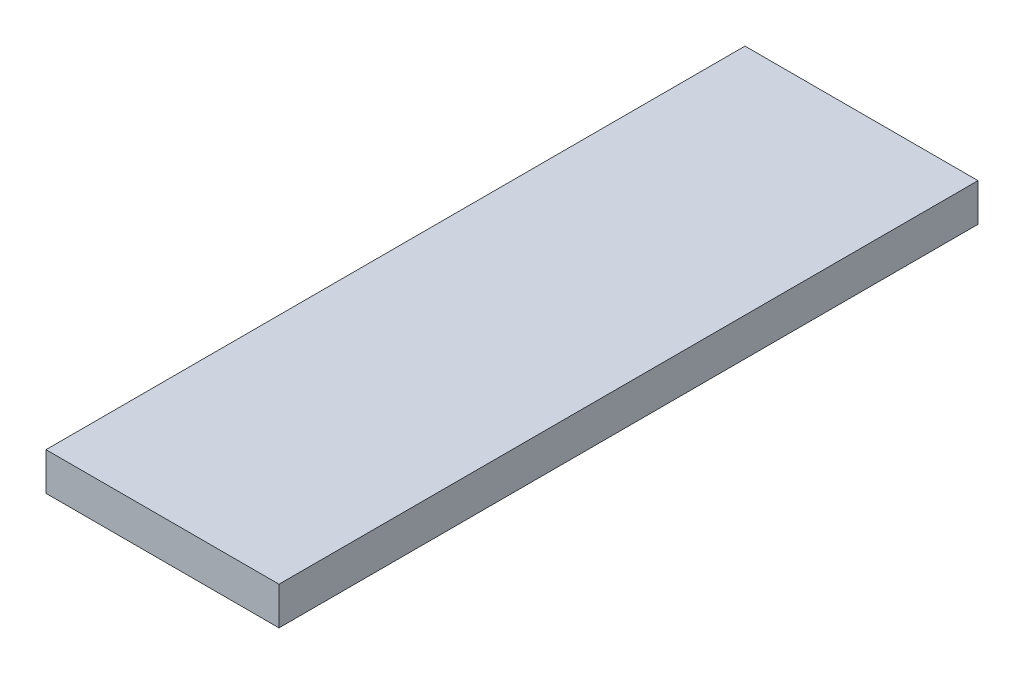
SolidWorks part; units mm, degrees
ref_plane "Front Plane" through (0, 0, 0) normal (0, 0, 1) x (1, 0, 0)
ref_plane "Top Plane" through (0, 0, 0) normal (0, 1, 0) x (1, 0, 0)
ref_plane "Right Plane" through (0, 0, 0) normal (1, 0, 0) x (0, 0, -1)
sketch "Sketch1" plane through (0, 0, 0) normal (0, 1, 0) x (1, 0, 0)
  line L1 (0, 0) -> (40, 0)
  line L2 (0, 0) -> (0, 120)
  line L3 (0, 120) -> (40, 120)
  line L4 (40, 0) -> (40, 120)
extrude "Boss-Extrude1" add sketch "Sketch1" along normal blind 6.5
